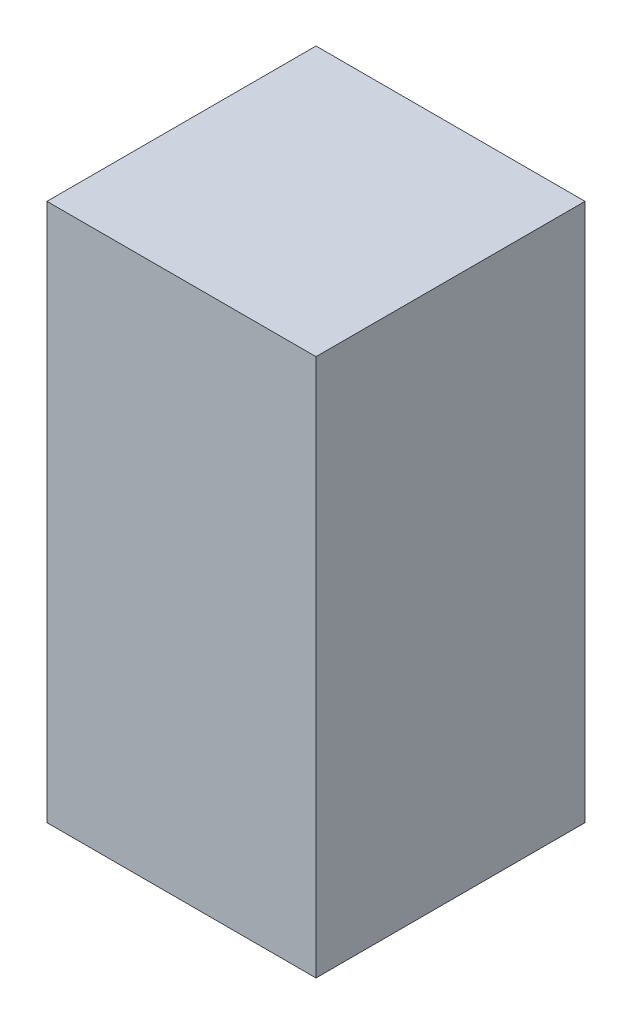
SolidWorks part; units mm, degrees
ref_plane "Alzado" through (0, 0, 0) normal (0, 0, 1) x (1, 0, 0)
ref_plane "Planta" through (0, 0, 0) normal (0, 1, 0) x (1, 0, 0)
ref_plane "Vista lateral" through (0, 0, 0) normal (1, 0, 0) x (0, 0, -1)
sketch "Sketch1" plane through (0, 0, 0) normal (0, 0, 1) x (1, 0, 0)
  line L1 (-7.5, -15) -> (7.5, -15)
  line L2 (-7.5, -15) -> (-7.5, 15)
  line L3 (-7.5, 15) -> (7.5, 15)
  line L4 (7.5, -15) -> (7.5, 15)
  line L5 (-7.5, -15) -> (7.5, 15) construction
  line L6 (-7.5, 15) -> (7.5, -15) construction
  point P0 (0, 0)
  dimension "D1" = 15
  dimension "D2" = 30
extrude "Boss-Extrude1" add sketch "Sketch1" along normal blind 15
